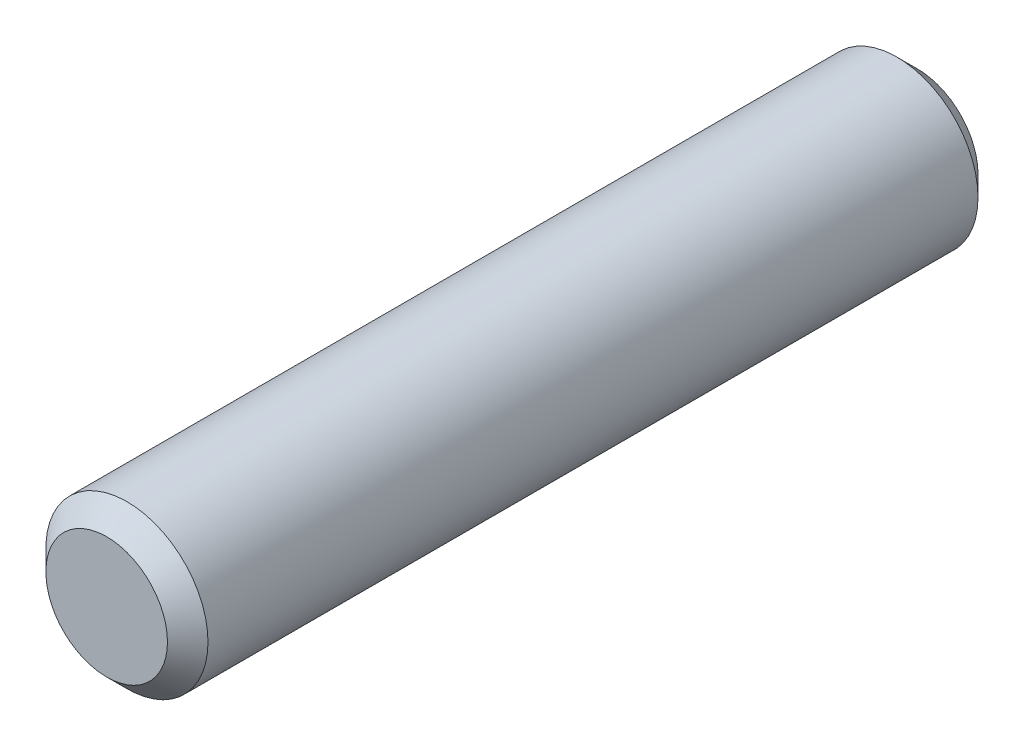
SolidWorks part; units mm, degrees
ref_plane "Plane1" through (0, 0, 0) normal (0, 0, 1) x (1, 0, 0)
ref_plane "Plane2" through (0, 0, 0) normal (0, 1, 0) x (1, 0, 0)
ref_plane "Plane3" through (0, 0, 0) normal (1, 0, 0) x (0, 0, -1)
sketch "Esquisse1" plane through (0, 0, 0) normal (0, 0, 1) x (1, 0, 0)
  circle A0 centre (0, 0) radius 1
  dimension "D1" = 2
extrude "Base-Extrusion" add sketch "Esquisse1" along normal blind 10
chamfer "Chanfrein1" distance 0.25 angle 45
